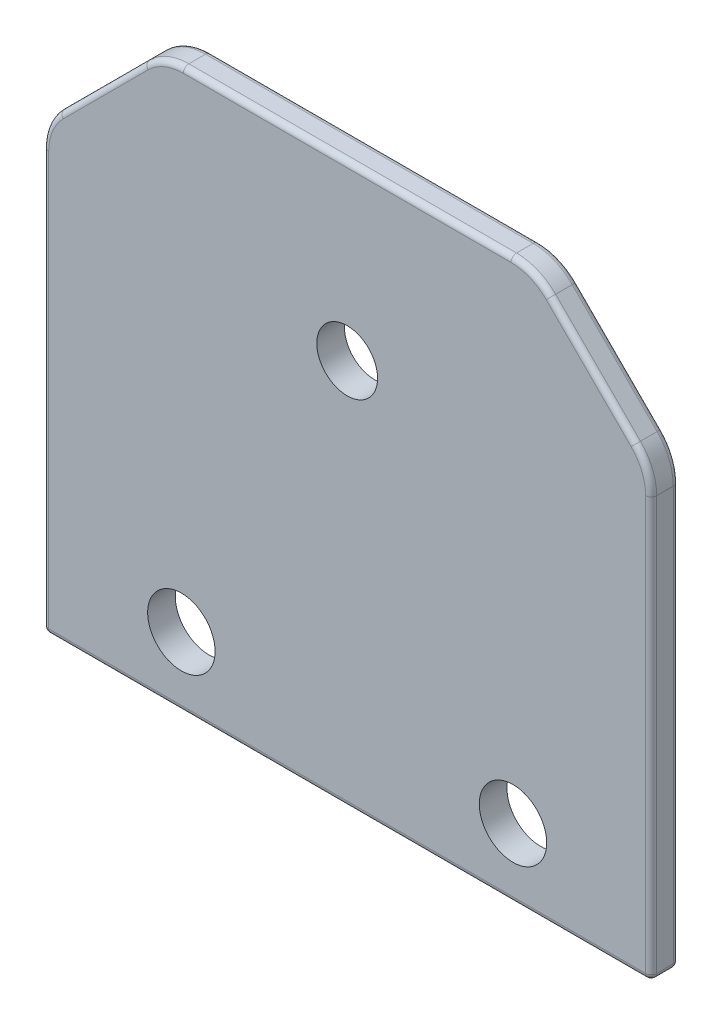
SolidWorks part; units mm, degrees
ref_plane "Front Plane" through (0, 0, 0) normal (0, 0, 1) x (1, 0, 0)
ref_plane "Top Plane" through (0, 0, 0) normal (0, 1, 0) x (1, 0, 0)
ref_plane "Right Plane" through (0, 0, 0) normal (1, 0, 0) x (0, 0, -1)
sketch "Sketch1" plane through (0, 0, 0) normal (0, 0, 1) x (1, 0, 0)
  line L0 (0, 0) -> (0, 12.5)
  line L1 (0, 0) -> (110, 0)
  line L2 (0, 0) -> (0, 80)
  line L3 (0, 80) -> (110, 80)
  line L4 (110, 0) -> (110, 80)
  line L5 (0, 80) -> (21.2132, 101.2132)
  line L6 (110, 80) -> (88.7868, 101.2132)
  line L7 (88.7868, 101.2132) -> (21.2132, 101.2132)
  line L8 (0, 80) -> (0, 70)
  line L9 (0, 0) -> (25, 0)
  line L10 (110, 0) -> (85, 0)
  circle A4 centre (55, 70) radius 5.5
  circle A5 centre (25, 12.5) radius 6.1
  circle A6 centre (85, 12.5) radius 6.1
  point P17 (0, 0)
  dimension "D7" = 11
  dimension "D10" = 12.2
  dimension "D11" = 12.2
  dimension "D6" = 12.5
  dimension "D8" = 25
  dimension "D9" = 10
  dimension "D12" = 55
  dimension "D13" = 12.5
  dimension "D14" = 25
  dimension "D1" = 110
  dimension "D2" = 80
  dimension "D3" = 67.5736
  dimension "D4" = 45
  dimension "D5" = 45
  dimension "0" = 30
extrude "Boss-Extrude1" add sketch "Sketch1" along normal blind 5 contours L6 L7 L5 L3 | L1 L4 L3 L2 L0
fillet "Fillet1" radius 10 4 edges at (110, 80, 2.5) (88.7868, 101.2132, 2.5) (0, 80, 2.5) (21.2132, 101.2132, 2.5)
fillet "Fillet2" radius 1 22 edges at (110, 37.9289, 0) (110, 37.9289, 5) (109.2388, 79.6847, 5) (109.2388, 79.6847, 0) (99.3934, 90.6066, 5) (99.3934, 90.6066, 0) (88.4715, 100.452, 5) (88.4715, 100.452, 0) (0, 37.9289, 5) (0, 37.9289, 0) (0.7612, 79.6847, 5) (0.7612, 79.6847, 0) (10.6066, 90.6066, 0) (10.6066, 90.6066, 5) (21.5285, 100.452, 5) (21.5285, 100.452, 0) (110, 0, 2.5) (55, 0, 0) (55, 0, 5) (0, 0, 2.5) (55, 101.2132, 5) (55, 101.2132, 0)
sketch "Sketch3" plane through (0, 0, 5) normal (0, 0, 1) x (1, 0, 0)
  circle A0 centre (25, 12.5) radius 6.1
  circle A1 centre (85, 12.5) radius 6.1
